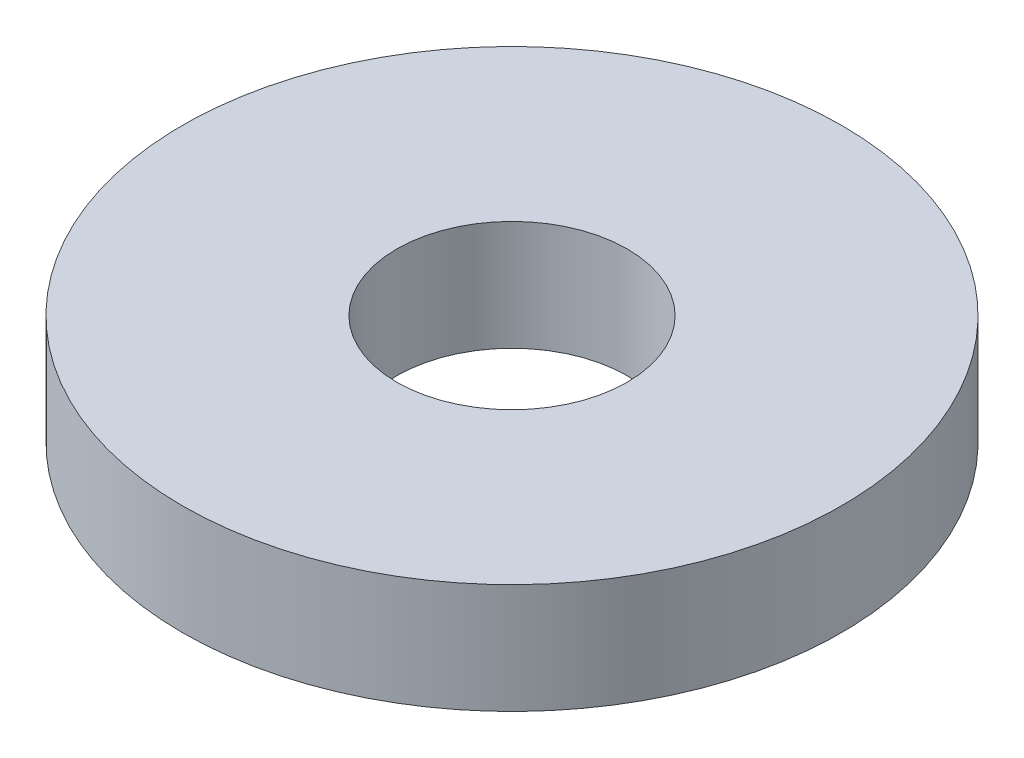
SolidWorks part; units mm, degrees
material "3.1355 (EN-AW 2024)"
ref_plane "Спереди" through (0, 0, 0) normal (0, 0, 1) x (1, 0, 0)
ref_plane "Сверху" through (0, 0, 0) normal (0, 1, 0) x (1, 0, 0)
ref_plane "Справа" through (0, 0, 0) normal (1, 0, 0) x (0, 0, -1)
sketch "Эскиз1" plane through (0, 0, 0) normal (0, 1, 0) x (1, 0, 0)
  circle A0 centre (0, 0) radius 6
  circle A1 centre (0, 0) radius 2.1
  dimension "D1" = 12
  dimension "D2" = 4.2
extrude "Бобышка-Вытянуть1" add sketch "Эскиз1" along normal blind 2
